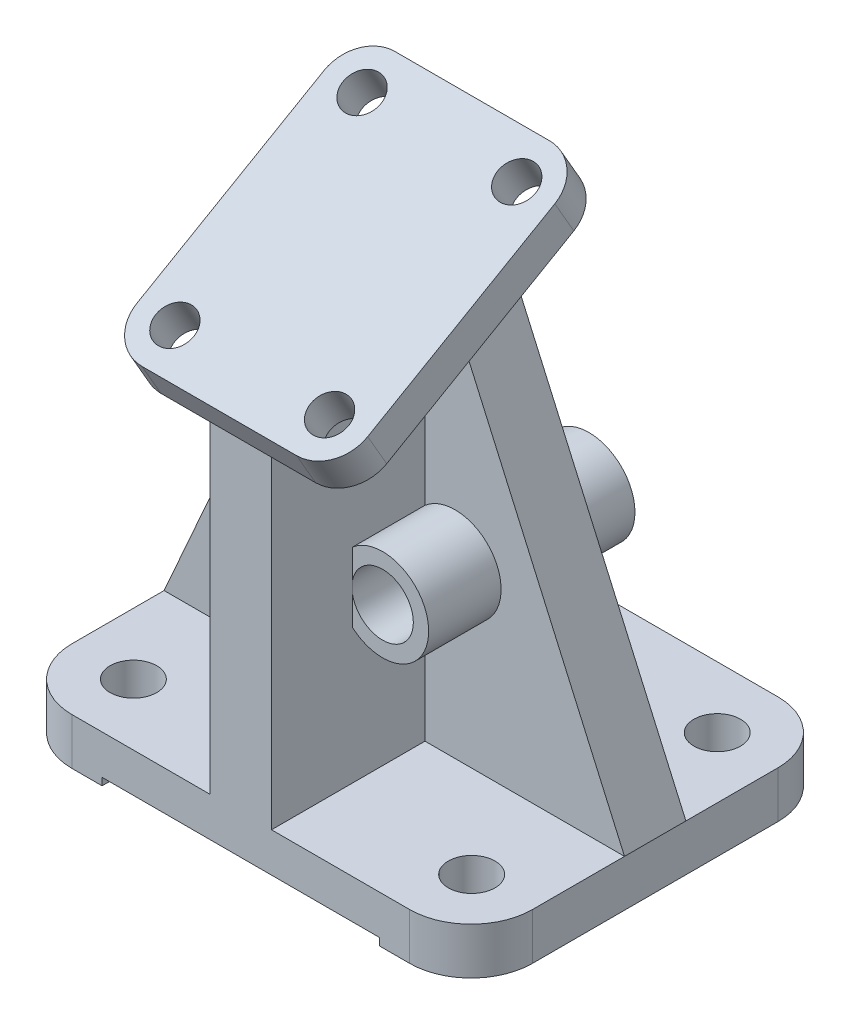
SolidWorks part; units mm, degrees
material "Oro puro"
ref_plane "Alzado" through (0, 0, 0) normal (0, 0, 1) x (1, 0, 0)
ref_plane "Planta" through (0, 0, 0) normal (0, 1, 0) x (1, 0, 0)
ref_plane "Vista lateral" through (0, 0, 0) normal (1, 0, 0) x (0, 0, -1)
sketch "Croquis3" plane through (0, 0, 0) normal (0, 1, 0) x (1, 0, 0)
  line L1 (-47.625, 38.1) -> (47.625, 38.1)
  line L2 (-47.625, 38.1) -> (-47.625, -38.1)
  line L3 (-47.625, -38.1) -> (47.625, -38.1)
  line L4 (47.625, 38.1) -> (47.625, -38.1)
  line L5 (-47.625, 38.1) -> (47.625, -38.1) construction
  line L6 (-47.625, -38.1) -> (47.625, 38.1) construction
  point P0 (0, 0)
  dimension "D1" = 76.2
  dimension "D2" = 95.25
extrude "Saliente-Extruir1" add sketch "Croquis3" along normal blind 9.652
fillet "Redondeo1" radius 12.7 4 edges at (47.625, 4.826, 38.1) (47.625, 4.826, -38.1) (-47.625, 4.826, -38.1) (-47.625, 4.826, 38.1)
sketch "Croquis4" plane through (0, 9.652, 0) normal (0, 1, 0) x (1, 0, 0)
  line L0 (-34.925, -38.1) -> (34.925, -38.1) construction
  circle A0 centre (-34.925, -25.4) radius 4.826
  arc A1 (-47.625, -25.4) -> (-34.925, -38.1) centre (-34.925, -25.4) ccw construction
  circle A2 centre (35.052, -25.4) radius 4.826
  circle A3 centre (35.052, 25.4) radius 4.826
  circle A4 centre (-34.925, 25.4) radius 4.826
  point P7 (0, -38.1)
  dimension "Orificios de la Base" = 9.652
  dimension "D4" = 35.052
  dimension "D2" = 2
  dimension "D3" = 2
extrude "Cortar-Extruir2" cut sketch "Croquis4" against normal blind 9.652
sketch "Croquis6" plane through (0, 9.652, 0) normal (0, 1, 0) x (1, 0, 0)
  line L0 (0, -38.1) -> (0, 38.1) construction
  line L1 (-34.925, -38.1) -> (34.925, -38.1) construction
  line L2 (34.925, 38.1) -> (-34.925, 38.1) construction
  line L4 (-6.35, 4.9177) -> (6.35, 4.9177)
  line L5 (-6.35, 4.9177) -> (-6.35, -38.1)
  line L6 (-6.35, -38.1) -> (6.35, -38.1)
  line L7 (6.35, 4.9177) -> (6.35, -38.1)
  line L8 (-6.35, 4.9177) -> (6.35, -38.1) construction
  line L9 (-6.35, -38.1) -> (6.35, 4.9177) construction
  point P6 (0, -16.5911)
  dimension "D1" = 12.7
extrude "Saliente-Extruir3" add sketch "Croquis6" along normal blind 67.564
sketch "Croquis8" plane through (0, 9.652, 0) normal (0, 1, 0) x (1, 0, 0)
  line L0 (47.625, -25.4) -> (47.625, 25.4) construction
  line L1 (-47.625, -6.35) -> (47.625, -6.35)
  line L2 (-47.625, -6.35) -> (-47.625, 6.35)
  line L3 (-47.625, 6.35) -> (47.625, 6.35)
  line L4 (47.625, -6.35) -> (47.625, 6.35)
  line L5 (-47.625, -6.35) -> (47.625, 6.35) construction
  line L6 (-47.625, 6.35) -> (47.625, -6.35) construction
  point P0 (0, 0)
  dimension "D1" = 12.7
extrude "Saliente-Extruir4" add sketch "Croquis8" along normal blind 93.218
ref_plane "Plano2" through (0, 74.4098, 42.9605) normal (0, 0.866, 0.5) x (1, 0, 0)
sketch "Croquis23" plane through (0, 74.4098, 42.9605) normal (0, 0.866, 0.5) x (1, 0, 0)
  line L0 (0, 5.0116) -> (23.876, 5.0116)
  line L1 (0, 5.0116) -> (-23.876, 5.0116)
  line L2 (-23.876, 5.0116) -> (-23.876, 65.4636)
  line L3 (-23.876, 65.4636) -> (23.876, 65.4636)
  line L4 (23.876, 65.4636) -> (23.876, 5.0116)
  dimension "D1" = 23.876
  dimension "D2" = 23.876
  dimension "D3" = 60.452
extrude "Saliente-Extruir10" add sketch "Croquis23" along normal blind 7.874 separate body
sketch "Croquis11" plane through (0, 0, -6.35) normal (0, 0, -1) x (-1, 0, 0)
  line L0 (0, 102.87) -> (-6.35, 102.87)
  line L1 (-47.625, 102.87) -> (47.625, 102.87) construction
  line L2 (0, 102.87) -> (6.35, 102.87)
  line L3 (-6.35, 102.87) -> (-47.625, 9.652)
  line L4 (-47.625, 9.652) -> (-47.625, 102.87)
  line L5 (-47.625, 102.87) -> (-6.35, 102.87)
  dimension "D1" = 6.35
  dimension "D2" = 6.35
extrude "Cortar-Extruir8" cut sketch "Croquis11" against normal blind 12.7 contours L3 L4 L5
sketch "Croquis13" plane through (0, 0, -6.35) normal (0, 0, -1) x (-1, 0, 0)
  line L0 (-6.35, 102.87) -> (6.35, 102.87)
  line L1 (-6.35, 102.87) -> (47.625, 102.87) construction
  line L2 (6.35, 102.87) -> (47.625, 9.652)
  line L3 (47.625, 9.652) -> (47.625, 102.87)
  line L4 (47.625, 102.87) -> (6.35, 102.87)
  dimension "D1" = 12.7
sketch "Croquis14" plane through (0, 0, 6.35) normal (0, 0, 1) x (1, 0, 0)
  line L0 (6.35, 9.652) -> (47.625, 9.652) construction
  circle A0 centre (12.573, 44.704) radius 9.525
  dimension "D3" = 19.05
  dimension "D1" = 35.052
  dimension "D2" = 35.052
extrude "Saliente-Extruir7" add sketch "Croquis14" along normal blind 14.986
sketch "Croquis16" plane through (0, 0, 6.35) normal (0, 0, 1) x (1, 0, 0)
  circle A0 centre (12.573, 44.704) radius 9.525
  dimension "D1" = 19.05
extrude "Saliente-Extruir8" add sketch "Croquis16" against normal blind 27.686
sketch "Croquis17" plane through (0, 0, 21.336) normal (0, 0, 1) x (1, 0, 0)
  circle A0 centre (12.573, 44.704) radius 6.35
  arc A1 (6.35, 37.4929) -> (6.35, 51.9151) centre (12.573, 44.704) ccw construction
  dimension "Orificio del Tubo" = 12.7
extrude "Cortar-Extruir10" cut sketch "Croquis17" against normal through all
extrude "Cortar-Extruir13" cut sketch "Croquis13" against normal blind 12.7 contours L2 L3 L4
fillet "Redondeo3" radius 7.874 4 edges at (-23.876, 80.3251, 40.5888) (-23.876, 110.5511, -11.7642) (23.876, 110.5511, -11.7642) (23.876, 80.3251, 40.5888)
sketch "Croquis24" plane through (0, 81.2289, 46.8975) normal (0, 0.866, 0.5) x (1, 0, 0)
  circle A0 centre (-16.002, 12.8856) radius 3.937
  arc A1 (-23.876, 12.8856) -> (-16.002, 5.0116) centre (-16.002, 12.8856) ccw construction
  circle A2 centre (16.002, 12.8856) radius 3.937
  arc A3 (16.002, 5.0116) -> (23.876, 12.8856) centre (16.002, 12.8856) ccw construction
  circle A4 centre (-16.002, 57.5896) radius 3.937
  circle A5 centre (16.002, 57.5896) radius 3.937
  arc A6 (23.876, 57.5896) -> (16.002, 65.4636) centre (16.002, 57.5896) ccw construction
  point P2 (-16.002, 12.8856)
  dimension "Orificios de la Cara Superior" = 7.874
  dimension "D2" = 2
  dimension "D3" = 2
extrude "Cortar-Extruir14" cut sketch "Croquis24" against normal blind 12.7
sketch "Croquis25" plane through (0, 0, 6.35) normal (0, 0, 1) x (1, 0, 0)
  line L0 (6.35, 77.216) -> (6.35, 99.2144)
  line L1 (-6.35, 77.216) -> (-6.35, 99.2144)
  line L3 (-6.35, 77.216) -> (6.35, 77.216)
  line L4 (-6.35, 99.2144) -> (6.35, 99.2144)
extrude "Saliente-Extruir11" add sketch "Croquis25" along normal blind 31.75
sketch "Croquis26" plane through (6.35, 0, 0) normal (1, 0, 0) x (0, 0, -1)
  line L0 (-15.7456, 99.2144) -> (-38.1, 99.2144)
  line L1 (-38.1, 99.2144) -> (-38.1, 86.3081)
  line L2 (-38.1, 86.3081) -> (-15.7456, 99.2144)
extrude "Cortar-Extruir15" cut sketch "Croquis26" against normal blind 31.75
sketch "Croquis27" plane through (0, 0, 38.1) normal (0, 0, 1) x (1, 0, 0)
  line L0 (-28.702, 0) -> (28.702, 0)
  line L1 (-34.925, 0) -> (34.925, 0) construction
  line L2 (-28.702, 0) -> (-28.702, 1.524)
  line L3 (-28.702, 1.524) -> (28.702, 1.524)
  line L4 (28.702, 1.524) -> (28.702, 0)
  point P5 (0, 0)
  dimension "D1" = 57.404
  dimension "D2" = 1.524
extrude "Cortar-Extruir16" cut sketch "Croquis27" against normal through all
